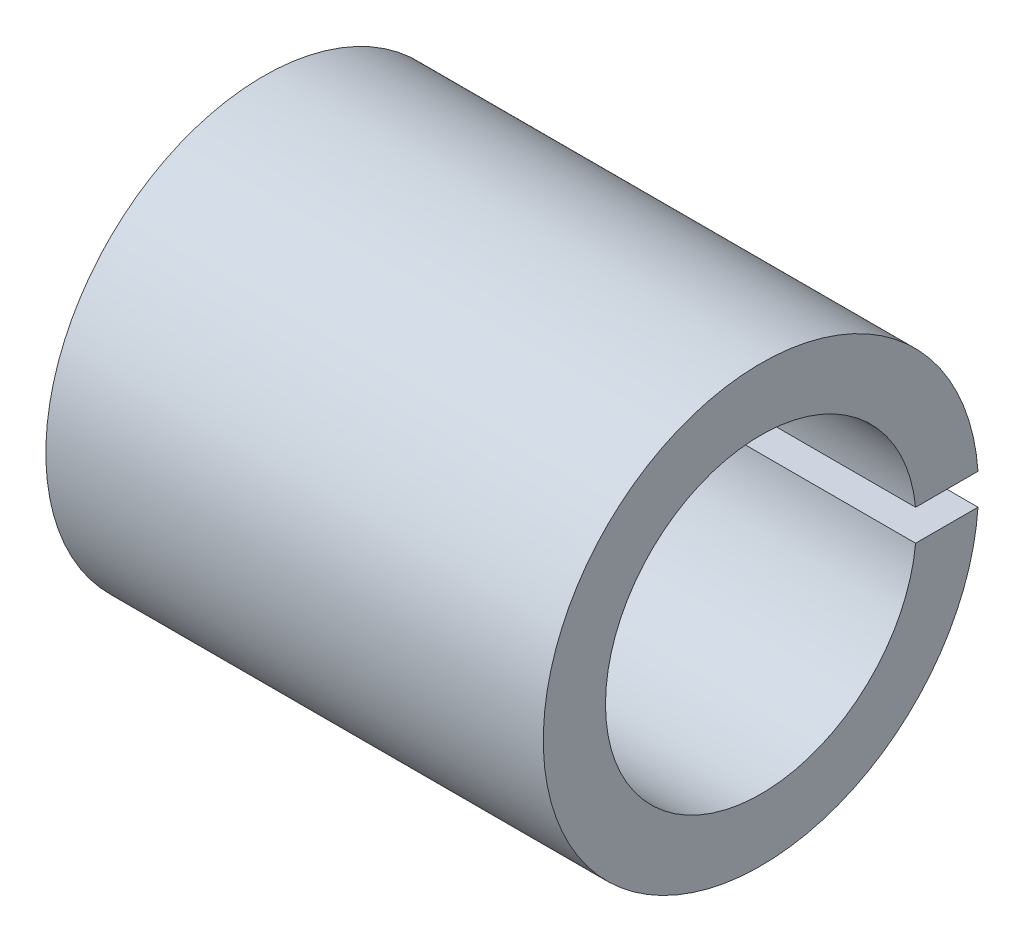
SolidWorks part; units mm, degrees
material "1060 Alloy"
ref_plane "Front Plane" through (0, 0, 0) normal (0, 0, 1) x (1, 0, 0)
ref_plane "Top Plane" through (0, 0, 0) normal (0, 1, 0) x (1, 0, 0)
ref_plane "Right Plane" through (0, 0, 0) normal (1, 0, 0) x (0, 0, -1)
sketch "Sketch1" plane through (0, 0, 0) normal (1, 0, 0) x (0, 0, -1)
  line L0 (-1000, 0) -> (49000, 0) construction
  line L1 (0, -1000) -> (0, 49000) construction
  line L2 (4.9749, 0.5) -> (6.9821, 0.5)
  line L3 (4.9749, -0.5) -> (6.9821, -0.5)
  arc A0 (6.9821, 0.5) -> (6.9821, -0.5) centre (0, 0) ccw
  arc A1 (4.9749, 0.5) -> (4.9749, -0.5) centre (0, 0) ccw
  point P10 (4.9254, 0.8607)
  point P11 (6.9415, 0.9029)
  dimension "D1" = 10
  dimension "D2" = 14
  dimension "D3" = 1
extrude "Boss-Extrude1" add sketch "Sketch1" along normal mid plane 16
